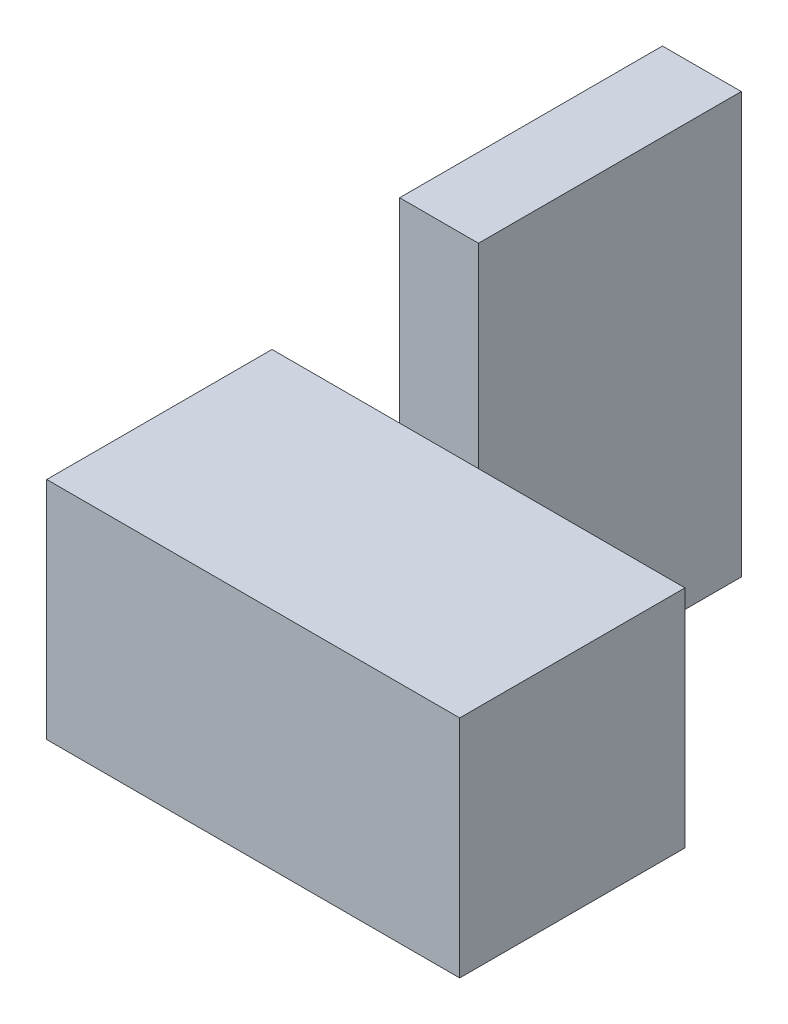
SolidWorks part; units mm, degrees
ref_plane "Front Plane" through (0, 0, 0) normal (0, 0, 1) x (1, 0, 0)
ref_plane "Top Plane" through (0, 0, 0) normal (0, 1, 0) x (1, 0, 0)
ref_plane "Right Plane" through (0, 0, 0) normal (1, 0, 0) x (0, 0, -1)
other "Configuration Table"
sketch "Sketch1" plane through (0, 0, 0) normal (0, 1, 0) x (1, 0, 0)
  line L1 (27.5, 15) -> (-27.5, 15)
  line L2 (27.5, 15) -> (27.5, -15)
  line L3 (27.5, -15) -> (-27.5, -15)
  line L4 (-27.5, 15) -> (-27.5, -15)
  line L5 (27.5, 15) -> (-27.5, -15) construction
  line L6 (27.5, -15) -> (-27.5, 15) construction
  point P0 (0, 0)
  dimension "D1" = 55
  dimension "D2" = 30
extrude "Boss-Extrude1" add sketch "Sketch1" along normal blind 30
sketch "Sketch2" plane through (0, 0, 15) normal (0, 0, 1) x (1, 0, 0)
  line L1 (-27.5, 0) -> (27.5, 0) construction
  line L4 (0, 56) -> (-10.5, 56)
  line L5 (-10.5, 56) -> (-10.5, 0)
  line L8 (-10.5, 0) -> (0, 0)
  line L9 (-27.5, 30) -> (-27.5, 0) construction
  line L12 (0, 56) -> (0, 0)
  dimension "D1" = 17
  dimension "D3" = 56
extrude "Boss-Extrude2" add sketch "Sketch2" along normal blind 35
sketch "Sketch3" plane through (0, 0, 50) normal (0, 0, 1) x (1, 0, 0)
  line L1 (-2.5, 14) -> (-8, 14)
  line L2 (-2.5, 14) -> (-2.5, 3)
  line L3 (-2.5, 3) -> (-8, 3)
  line L4 (-8, 14) -> (-8, 3)
  line L5 (-2.5, 14) -> (-8, 3) construction
  line L6 (-2.5, 3) -> (-8, 14) construction
  line L7 (-2.5, 53) -> (-8, 53)
  line L8 (-2.5, 53) -> (-2.5, 42)
  line L9 (-2.5, 42) -> (-8, 42)
  line L10 (-8, 53) -> (-8, 42)
  line L11 (-2.5, 53) -> (-8, 42) construction
  line L12 (-2.5, 42) -> (-8, 53) construction
  line L14 (-10.5, 56) -> (-10.5, 0) construction
  line L15 (-10.5, 0) -> (0, 0) construction
  line L16 (0, 56) -> (-10.5, 56) construction
  point P0 (-5.25, 8.5)
  point P5 (-5.25, 47.5)
  point P10 (-2.5, 5.5996)
  point P11 (-5.25, 3)
  point P18 (-7.2696, 42)
  dimension "D1" = 11
  dimension "D2" = 5.5
  dimension "D3" = 5.25
  dimension "D4" = 3
  dimension "D5" = 3
  dimension "D6" = 5.25
extrude "Cut-Extrude1" cut sketch "Sketch3" against normal blind 22
mirror "Mirror1" about plane through (0, 0, 50) normal (0, 0, 1) of bodies 106
delete or keep bodies "Body-Delete/Keep 1" type delete bodies bodies 106
